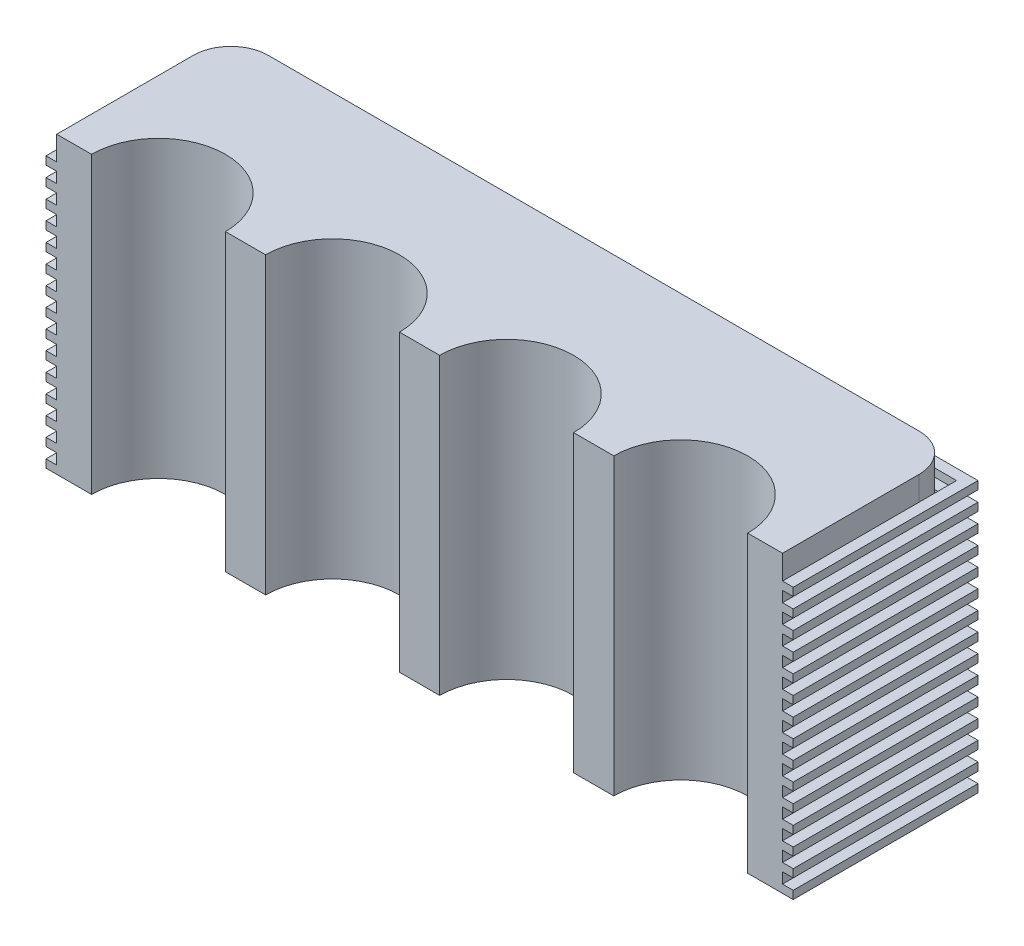
SolidWorks part; units mm, degrees
ref_plane "Ön Düzlem" through (0, 0, 0) normal (0, 0, 1) x (1, 0, 0)
ref_plane "Üst Düzlem" through (0, 0, 0) normal (0, 1, 0) x (1, 0, 0)
ref_plane "Sağ Düzlem" through (0, 0, 0) normal (1, 0, 0) x (0, 0, -1)
sketch "Çizim1" plane through (0, 0, 0) normal (0, 1, 0) x (1, 0, 0)
  line L0 (-154.5259, 89.4231) -> (124.4741, 89.4231)
  line L1 (124.4741, 89.4231) -> (124.4741, 20.4231)
  line L3 (-154.5259, 20.4231) -> (-154.5259, 89.4231)
  line L21 (-154.5259, 20.4231) -> (124.4741, 20.4231)
extrude "Yükseklik-Ekstrüzyon2" add sketch "Çizim1" along normal blind 110
sketch "Çizim2" plane through (0, 110, 0) normal (0, 1, 0) x (1, 0, 0)
  line L1 (-154.5259, 20.4231) -> (124.4741, 20.4231) construction
  line L2 (-137.5259, 20.4231) -> (-87.5259, 20.4231)
  line L5 (-72.5259, 20.4231) -> (-22.5259, 20.4231)
  line L7 (-7.5259, 20.4231) -> (42.4741, 20.4231)
  line L9 (57.4741, 20.4231) -> (107.4741, 20.4231)
  arc A0 (-87.5259, 20.4231) -> (-137.5259, 20.4231) centre (-112.5259, 20.4231) ccw
  arc A1 (-22.5259, 20.4231) -> (-72.5259, 20.4231) centre (-47.5259, 20.4231) ccw
  arc A2 (42.4741, 20.4231) -> (-7.5259, 20.4231) centre (17.4741, 20.4231) ccw
  arc A3 (107.4741, 20.4231) -> (57.4741, 20.4231) centre (82.4741, 20.4231) ccw
extrude "Kes-Ekstrüzyon1" cut sketch "Çizim2" against normal blind 110
sketch "Çizim10" plane through (0, 0, -20.4231) normal (0, 0, 1) x (1, 0, 0)
  line L0 (124.4741, 110) -> (124.4741, 101)
  line L1 (124.4741, 110) -> (124.4741, 0) construction
  line L2 (124.4741, 101) -> (120.4741, 101)
  line L3 (120.4741, 101) -> (120.4741, 110)
  line L5 (107.4741, 110) -> (124.4741, 110) construction
  line L6 (120.4741, 110) -> (124.4741, 110)
extrude "Kes-Ekstrüzyon5" cut sketch "Çizim10" against normal blind 290
sketch "Çizim11" plane through (120.4741, 0, 0) normal (1, 0, 0) x (0, 0, -1)
  line L0 (89.4231, 110) -> (89.4231, 101)
  line L1 (89.4231, 101) -> (85.4231, 101)
  line L2 (89.4231, 101) -> (20.4231, 101) construction
  line L3 (85.4231, 101) -> (85.4231, 110)
  line L4 (20.4231, 110) -> (89.4231, 110) construction
  line L5 (85.4231, 110) -> (89.4231, 110)
extrude "Kes-Ekstrüzyon6" cut sketch "Çizim11" against normal blind 290
sketch "Çizim12" plane through (0, 0, -85.4231) normal (0, 0, -1) x (-1, 0, 0)
  line L0 (154.5259, 110) -> (154.5259, 101)
  line L1 (154.5259, 101) -> (150.5259, 101)
  line L2 (154.5259, 101) -> (-120.4741, 101) construction
  line L3 (150.5259, 101) -> (150.5259, 110)
  line L4 (154.5259, 110) -> (-120.4741, 110) construction
  line L5 (150.5259, 110) -> (154.5259, 110)
extrude "Kes-Ekstrüzyon7" cut sketch "Çizim12" against normal blind 290
sketch "Çizim14" plane through (0, 0, -89.4231) normal (0, 0, -1) x (-1, 0, 0)
  line L1 (-124.4741, 101) -> (-124.4741, 0) construction
  line L2 (-124.4741, 3) -> (-124.4741, 6)
  line L3 (-124.4741, 3) -> (-120.4741, 3)
  line L4 (-120.4741, 3) -> (-120.4741, 6)
  line L5 (-120.4741, 6) -> (-124.4741, 6)
extrude "Kes-Ekstrüzyon8" cut sketch "Çizim14" against normal blind 290
sketch "Çizim15" plane through (120.4741, 0, 0) normal (1, 0, 0) x (0, 0, -1)
  line L0 (89.4231, 6) -> (89.4231, 3)
  line L1 (89.4231, 3) -> (85.4231, 3)
  line L2 (20.4231, 3) -> (89.4231, 3) construction
  line L3 (85.4231, 3) -> (85.4231, 6)
  line L4 (20.4231, 6) -> (89.4231, 6) construction
  line L5 (85.4231, 6) -> (89.4231, 6)
extrude "Kes-Ekstrüzyon9" cut sketch "Çizim15" against normal blind 290
sketch "Çizim16" plane through (0, 0, -85.4231) normal (0, 0, -1) x (-1, 0, 0)
  line L0 (154.5259, 3) -> (150.5259, 3)
  line L1 (-124.4741, 3) -> (154.5259, 3) construction
  line L2 (150.5259, 3) -> (150.5259, 6)
  line L3 (154.5259, 6) -> (-124.4741, 6) construction
  line L4 (150.5259, 6) -> (154.5259, 6)
  line L6 (154.5259, 6) -> (154.5259, 3)
  dimension "D1" = 3
extrude "Kes-Ekstrüzyon12" cut sketch "Çizim16" against normal blind 290
sketch "Çizim17" plane through (-154.5259, 0, 0) normal (-1, 0, 0) x (0, 0, 1)
  line L0 (-85.4231, 101) -> (-85.4231, 6)
  line L1 (-89.4231, 6) -> (-20.4231, 6) construction
  line L2 (-20.4231, 6) -> (-85.4231, 6) construction
  line L3 (-85.4231, 6) -> (-89.4231, 6)
  line L4 (-89.4231, 6) -> (-89.4231, 101)
  line L5 (-89.4231, 101) -> (-85.4231, 101)
extrude "Kes-Ekstrüzyon13" cut sketch "Çizim17" against normal blind 290
sketch "Çizim18" plane through (0, 0, -20.4231) normal (0, 0, 1) x (1, 0, 0)
  line L0 (-150.5259, 101) -> (-154.5259, 101)
  line L1 (-154.5259, 101) -> (-154.5259, 6)
  line L2 (-154.5259, 6) -> (-150.5259, 6)
  line L3 (-150.5259, 6) -> (-150.5259, 101)
extrude "Kes-Ekstrüzyon14" cut sketch "Çizim18" against normal blind 290
sketch "Çizim19" plane through (0, 0, -20.4231) normal (0, 0, 1) x (1, 0, 0)
  line L0 (120.4741, 101) -> (124.4741, 101)
  line L1 (124.4741, 101) -> (124.4741, 6)
  line L2 (124.4741, 6) -> (120.4741, 6)
  line L3 (120.4741, 6) -> (120.4741, 101)
extrude "Kes-Ekstrüzyon15" cut sketch "Çizim19" against normal blind 290
sketch "Çizim22" plane through (0, 110, 0) normal (0, 1, 0) x (1, 0, 0)
  line L0 (-150.5259, 20.4231) -> (-150.5259, 85.4231) construction
  line L1 (-150.5259, 85.4231) -> (120.4741, 85.4231) construction
  line L2 (-136.5259, 85.4231) -> (-150.5259, 85.4231)
  line L3 (-150.5259, 85.4231) -> (-150.5259, 71.4231)
  line L4 (120.4741, 20.4231) -> (120.4741, 85.4231) construction
  line L6 (120.4741, 71.4231) -> (120.4741, 85.4231)
  line L7 (120.4741, 85.4231) -> (106.4741, 85.4231)
  arc A0 (-136.5259, 85.4231) -> (-150.5259, 71.4231) centre (-136.5259, 71.4231) ccw
  arc A1 (120.4741, 71.4231) -> (106.4741, 85.4231) centre (106.4741, 71.4231) ccw
extrude "Kes-Ekstrüzyon17" cut sketch "Çizim22" against normal blind 107
sketch "Çizim23" plane through (0, 3, 0) normal (0, 1, 0) x (1, 0, 0)
  line L0 (-150.5259, 20.4231) -> (-154.5259, 20.4231)
  line L1 (-154.5259, 20.4231) -> (-154.5259, 89.4231)
  line L2 (-154.5259, 89.4231) -> (124.4741, 89.4231)
  line L3 (124.4741, 89.4231) -> (124.4741, 20.4231)
  line L4 (124.4741, 20.4231) -> (120.4741, 20.4231)
  line L5 (120.4741, 20.4231) -> (120.4741, 85.4231)
  line L6 (120.4741, 85.4231) -> (-150.5259, 85.4231)
  line L7 (-150.5259, 85.4231) -> (-150.5259, 20.4231)
extrude "Kes-Ekstrüzyon18" cut sketch "Çizim23" against normal blind 107
sketch "Çizim25" plane through (0, 0, 0) normal (0, -1, 0) x (1, 0, 0)
  line L0 (120.4741, -85.4231) -> (-150.5259, -85.4231) construction
  line L1 (120.4741, -20.4231) -> (120.4741, -85.4231) construction
  line L2 (120.4741, -71.4231) -> (120.4741, -85.4231)
  line L3 (120.4741, -85.4231) -> (106.4741, -85.4231)
  line L5 (-150.5259, -85.4231) -> (-136.5259, -85.4231)
  line L6 (-150.5259, -71.4231) -> (-150.5259, -85.4231)
  arc A0 (106.4741, -85.4231) -> (120.4741, -71.4231) centre (106.4741, -71.4231) ccw
  arc A1 (-136.5259, -85.4231) -> (-150.5259, -71.4231) centre (-136.5259, -71.4231) cw
extrude "Kes-Ekstrüzyon19" cut sketch "Çizim25" against normal blind 107
sketch "Çizim27" plane through (0, 0, 0) normal (0, -1, 0) x (1, 0, 0)
  line L0 (120.4741, -20.4231) -> (124.4741, -20.4231)
  line L1 (-150.5259, -20.4231) -> (-150.5259, -85.4231)
  line L2 (124.4741, -20.4231) -> (124.4741, -89.4231)
  line L3 (-150.5259, -20.4231) -> (-154.5259, -20.4231)
  line L4 (-150.5259, -85.4231) -> (120.4741, -85.4231)
  line L5 (-154.5259, -20.4231) -> (-154.5259, -89.4231)
  line L6 (-154.5259, -89.4231) -> (124.4741, -89.4231)
  line L7 (120.4741, -85.4231) -> (120.4741, -20.4231)
extrude "Yükseklik-Ekstrüzyon3" add sketch "Çizim27" against normal blind 3
pattern_linear "LÇoğaltma19" count 15 spacing 7 along (0, 1, 0) of "Yükseklik-Ekstrüzyon3"
